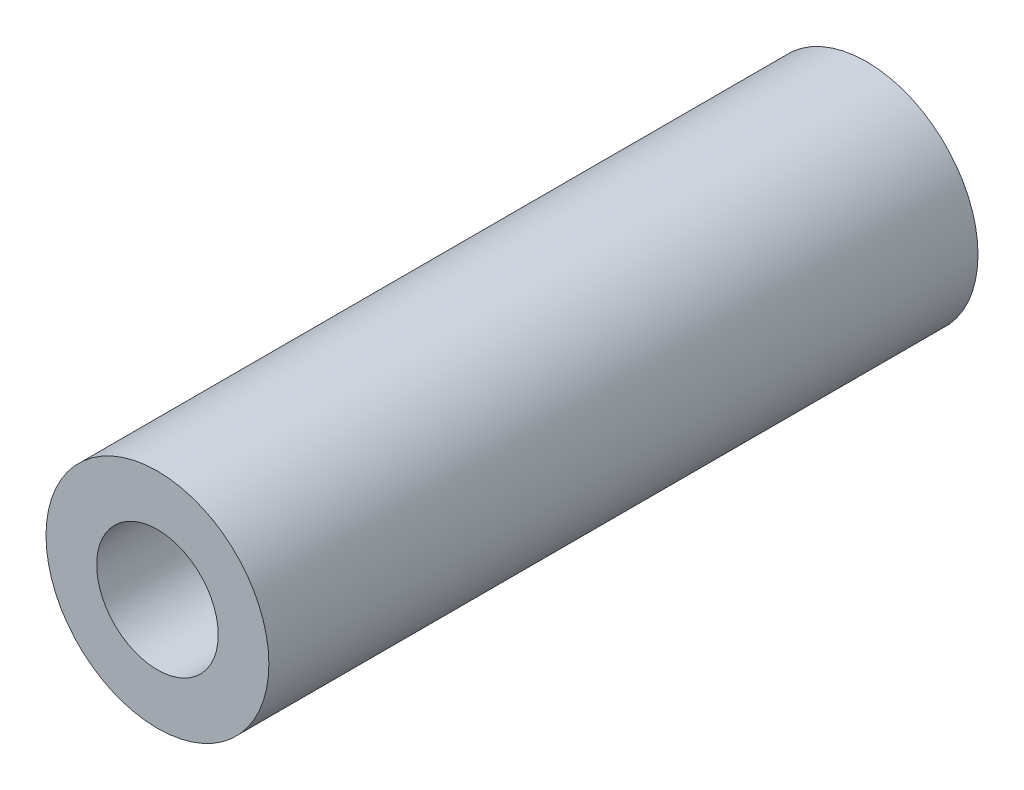
SolidWorks part; units mm, degrees
material "ABS"
ref_plane "Front Plane" through (0, 0, 0) normal (0, 0, 1) x (1, 0, 0)
ref_plane "Top Plane" through (0, 0, 0) normal (0, 1, 0) x (1, 0, 0)
ref_plane "Right Plane" through (0, 0, 0) normal (1, 0, 0) x (0, 0, -1)
sketch "Sketch1" plane through (0, 0, 0) normal (0, 0, 1) x (1, 0, 0)
  circle A0 centre (0, 0) radius 1.5
  circle A1 centre (0, 0) radius 2.75
  point P5 (-0.223, 0)
  dimension "D1" = 3
  dimension "D2" = 1.25
extrude "Boss-Extrude1" add sketch "Sketch1" along normal blind 17.5 contours A1 | A0
